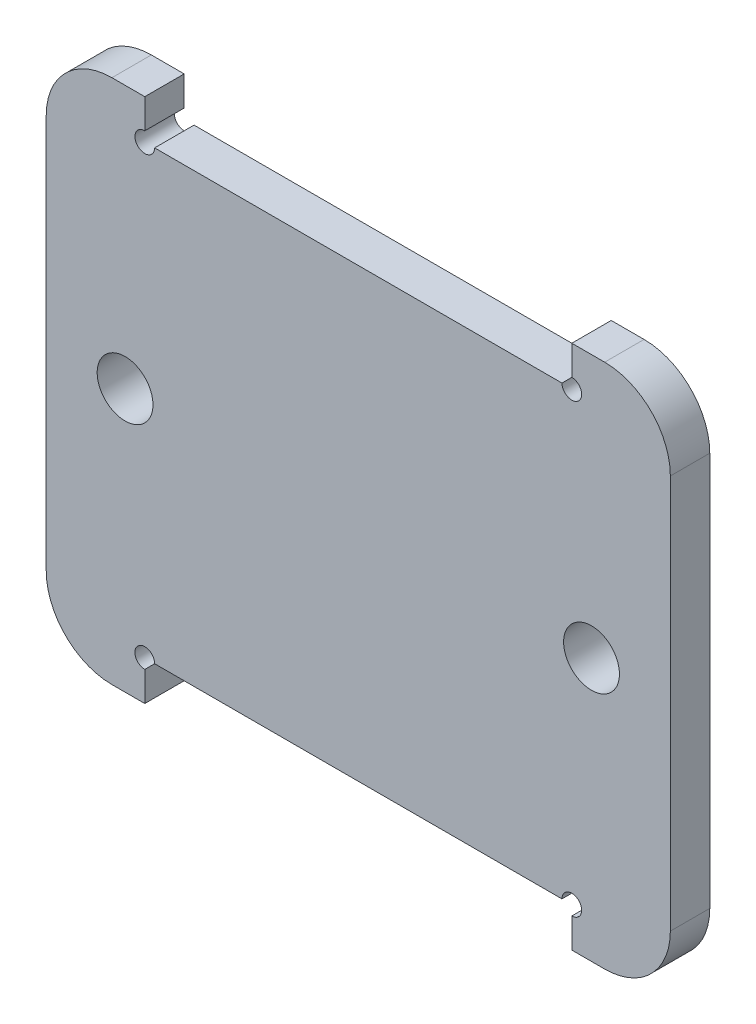
SolidWorks part; units mm, degrees
material "Plain Carbon Steel"
ref_plane "Front Plane" through (0, 0, 0) normal (0, 0, 1) x (1, 0, 0)
ref_plane "Top Plane" through (0, 0, 0) normal (0, 1, 0) x (1, 0, 0)
ref_plane "Right Plane" through (0, 0, 0) normal (1, 0, 0) x (0, 0, -1)
sketch "Sketch1" plane through (0, 0, 0) normal (0, 0, 1) x (1, 0, 0)
  line L0 (-347.5, 26) -> (-347.5, 94) construction
  line L1 (-330.5, 26) -> (-364.5, 26) construction
  line L2 (-364.5, 94) -> (-330.5, 94) construction
  line L3 (-380, 94) -> (-315, 94)
  line L4 (-315, 94) -> (-315, 100)
  line L6 (-315, 100) -> (-310, 100)
  line L7 (-300, 90) -> (-300, 30)
  line L8 (-310, 20) -> (-315, 20)
  line L9 (-315, 20) -> (-315, 26)
  line L10 (-325.5, 26) -> (-330.5, 26) construction
  line L12 (-315, 26) -> (-380, 26)
  line L13 (-300, 60) -> (-395, 60) construction
  line L14 (-380, 20) -> (-380, 26)
  line L15 (-385, 20) -> (-380, 20)
  line L16 (-395, 90) -> (-395, 30)
  line L17 (-380, 100) -> (-385, 100)
  line L18 (-380, 94) -> (-380, 100)
  line L19 (-315, 26) -> (-315, 20) construction
  line L20 (-325.5, 20) -> (-315, 20) construction
  line L21 (-315, 100) -> (-315, 94) construction
  arc A0 (-310, 100) -> (-300, 90) centre (-310, 90) cw
  arc A1 (-300, 30) -> (-310, 20) centre (-310, 30) cw
  circle A2 centre (-312, 60) radius 4.25
  circle A3 centre (-383, 60) radius 4.25
  arc A4 (-395, 30) -> (-385, 20) centre (-385, 30) ccw
  arc A5 (-385, 100) -> (-395, 90) centre (-385, 90) ccw
  point P29 (-347.5, 60)
  dimension "D1" = 10
  dimension "D2" = 8.5
  dimension "D3" = 5
  dimension "D4" = 12
extrude "Boss-Extrude1" add sketch "Sketch1" along normal blind 6
sketch "Sketch2" plane through (0, 0, 6) normal (0, 0, 1) x (1, 0, 0)
  line L0 (-347.5, 26) -> (-347.5, 94) construction
  line L1 (-380, 26) -> (-315, 26) construction
  line L2 (-315, 94) -> (-380, 94) construction
  line L3 (-300, 60) -> (-395, 60) construction
  line L4 (-300, 30) -> (-300, 90) construction
  line L5 (-395, 90) -> (-395, 30) construction
  circle A0 centre (-380, 26) radius 1.5
  circle A1 centre (-315, 26) radius 1.5
  circle A2 centre (-380, 94) radius 1.5
  circle A3 centre (-315, 94) radius 1.5
  dimension "D1" = 3
extrude "Cut-Extrude1" cut sketch "Sketch2" against normal through all
